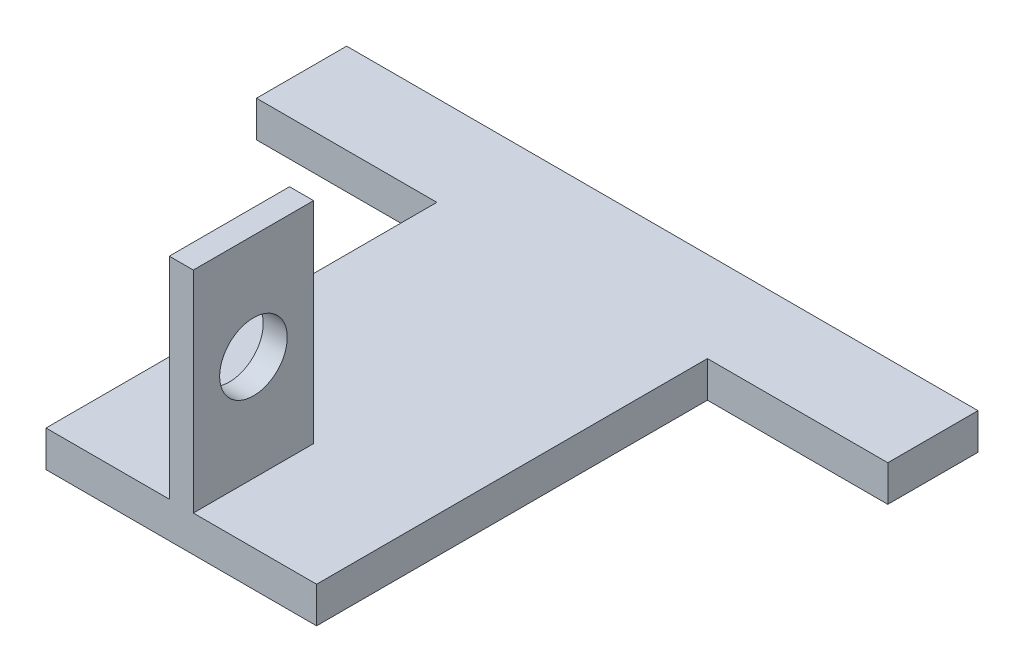
SolidWorks part; units mm, degrees
ref_plane "Front Plane" through (0, 0, 0) normal (0, 0, 1) x (1, 0, 0)
ref_plane "Top Plane" through (0, 0, 0) normal (0, 1, 0) x (1, 0, 0)
ref_plane "Right Plane" through (0, 0, 0) normal (1, 0, 0) x (0, 0, -1)
sketch "Sketch1" plane through (0, 0, 0) normal (0, 1, 0) x (1, 0, 0)
  line L0 (0, 16) -> (0, -16) construction
  line L1 (-9, -16) -> (9, -16)
  line L2 (-9, -16) -> (-9, 16)
  line L3 (-9, 16) -> (9, 16)
  line L4 (9, -16) -> (9, 16)
  line L5 (-9, -16) -> (9, 16) construction
  line L6 (-9, 16) -> (9, -16) construction
  line L7 (-9, 16) -> (-21, 16)
  line L8 (-9, 16) -> (-9, 10)
  line L9 (-9, 10) -> (-21, 10)
  line L10 (-21, 16) -> (-21, 10)
  line L11 (9, 10) -> (21, 10)
  line L12 (21, 16) -> (21, 10)
  line L13 (9, 16) -> (21, 16)
  line L14 (9, 16) -> (9, 10)
  point P0 (0, 0)
  dimension "D1" = 18
  dimension "D2" = 32
  dimension "D3" = 6
  dimension "D4" = 21
extrude "Boss-Extrude1" add sketch "Sketch1" along normal blind 2.4 contours L1 L4 L3 L2 | L7 L10 L9 L2 | L13 L4 L11 L12
sketch "Sketch4" plane through (0, 2.4, 0) normal (0, 1, 0) x (1, 0, 0)
  line L0 (0, 0) -> (0, -16) construction
  line L1 (-9, -16) -> (9, -16) construction
  line L3 (-0.8, -8) -> (0.8, -8)
  line L4 (-0.8, -8) -> (-0.8, -16)
  line L5 (-0.8, -16) -> (0.8, -16)
  line L6 (0.8, -8) -> (0.8, -16)
  line L7 (-0.8, -8) -> (0.8, -16) construction
  line L8 (-0.8, -16) -> (0.8, -8) construction
  point P5 (0, -12)
  dimension "D1" = 8
  dimension "D2" = 1.6
extrude "Boss-Extrude3" add sketch "Sketch4" along normal blind 14
sketch "Sketch5" plane through (-0.8, 0, 0) normal (-1, 0, 0) x (0, 0, 1)
  line L0 (12, 16.4) -> (12, 2.4) construction
  line L1 (8, 16.4) -> (16, 16.4) construction
  line L2 (8, 2.4) -> (16, 2.4) construction
  circle A0 centre (12, 9.4) radius 2.25
  dimension "D1" = 4.5
extrude "Cut-Extrude2" cut sketch "Sketch5" against normal up to next
